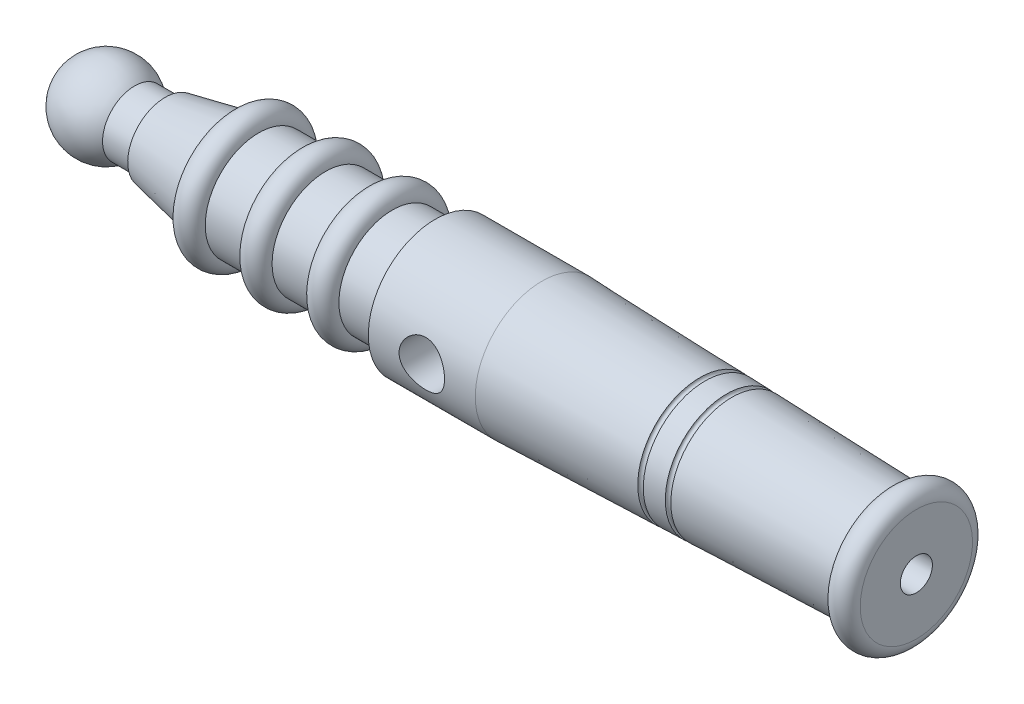
SolidWorks part; units mm, degrees
ref_plane "Płaszczyzna przednia" through (0, 0, 0) normal (0, 0, 1) x (1, 0, 0)
ref_plane "Płaszczyzna górna" through (0, 0, 0) normal (0, 1, 0) x (1, 0, 0)
ref_plane "Płaszczyzna prawa" through (0, 0, 0) normal (1, 0, 0) x (0, 0, -1)
sketch "Szkic2" plane through (0, 0, 0) normal (0, 0, 1) x (1, 0, 0)
  line L0 (0, 0) -> (109.5, 0)
  line L1 (109.5, 0) -> (109.5, 3)
  line L2 (109.5, 3) -> (159.5, 3)
  line L3 (159.5, 3) -> (159.5, 10.5)
  line L4 (154.5, 10.5002) -> (124.9832, 11.4083)
  line L5 (89.5, 12.5) -> (69.5, 12.5)
  line L6 (69.5, 12.5) -> (69.5, 10)
  line L8 (19, 7) -> (19, 6)
  line L9 (19, 6) -> (13.2915, 6)
  line L10 (69.5, 10) -> (61.5, 10)
  line L11 (31.5485, 9.5097) -> (19, 7)
  line L12 (44, 10) -> (36.5, 10)
  line L13 (56.5, 10) -> (49, 10)
  line L14 (118.986, 11.5928) -> (89.5, 12.5)
  line L15 (123.9837, 11.4391) -> (119.9856, 11.5621)
  line L16 (31.5485, 9.5097) -> (34, 10) construction
  line L17 (34, 10) -> (36.5, 10) construction
  arc A0 (0, 0) -> (13.2915, 6) centre (8, 0) cw
  arc A1 (159.5, 10.5) -> (154.5, 10.5002) centre (157, 10.5) ccw
  arc A2 (61.5, 10) -> (56.5, 10) centre (59, 10) ccw
  arc A3 (49, 10) -> (44, 10) centre (46.5, 10) ccw
  arc A4 (36.5, 10) -> (31.5485, 9.5097) centre (34, 10) ccw
  arc A5 (119.9856, 11.5621) -> (118.986, 11.5928) centre (119.4858, 11.5775) cw
  arc A6 (124.9832, 11.4083) -> (123.9837, 11.4391) centre (124.4834, 11.4237) cw
  point P12 (157.0001, 13)
  point P18 (19, 6.5)
  point P32 (89.5, 12.5)
  point P33 (154.5, 10.5)
  point P34 (0, 0)
  point P35 (2.7085, 6)
  point P36 (13.1982, 6.081)
  dimension "D3" = 2.5
  dimension "D9" = 8
  dimension "D15" = 2.5
  dimension "D19" = 2.5
  dimension "D21" = 0.5
  dimension "D2" = 3
  dimension "D4" = 10
  dimension "D5" = 65
  dimension "D6" = 20
  dimension "D7" = 35.5
  dimension "D8" = 6
  dimension "D10" = 11
  dimension "D11" = 15
  dimension "D12" = 10
  dimension "D13" = 7
  dimension "D14" = 12.5
  dimension "D16" = 8
  dimension "D17" = 20
  dimension "D18" = 10
  dimension "D20" = 5
  dimension "D22" = 30
  dimension "D23" = 7.5002
  dimension "D24" = 50
revolve "Obrót1" add sketch "Szkic2" angle 360 about L0
sketch "Szkic3" plane through (0, 0, 0) normal (0, 0, 1) x (1, 0, 0)
  circle A0 centre (79.5, 0) radius 4.25
  dimension "D1" = 8.5
  dimension "D2" = 10
extrude "Wytnij-wyciągnięcie1" cut sketch "Szkic3" against normal through all both and the other way through all contours A0
